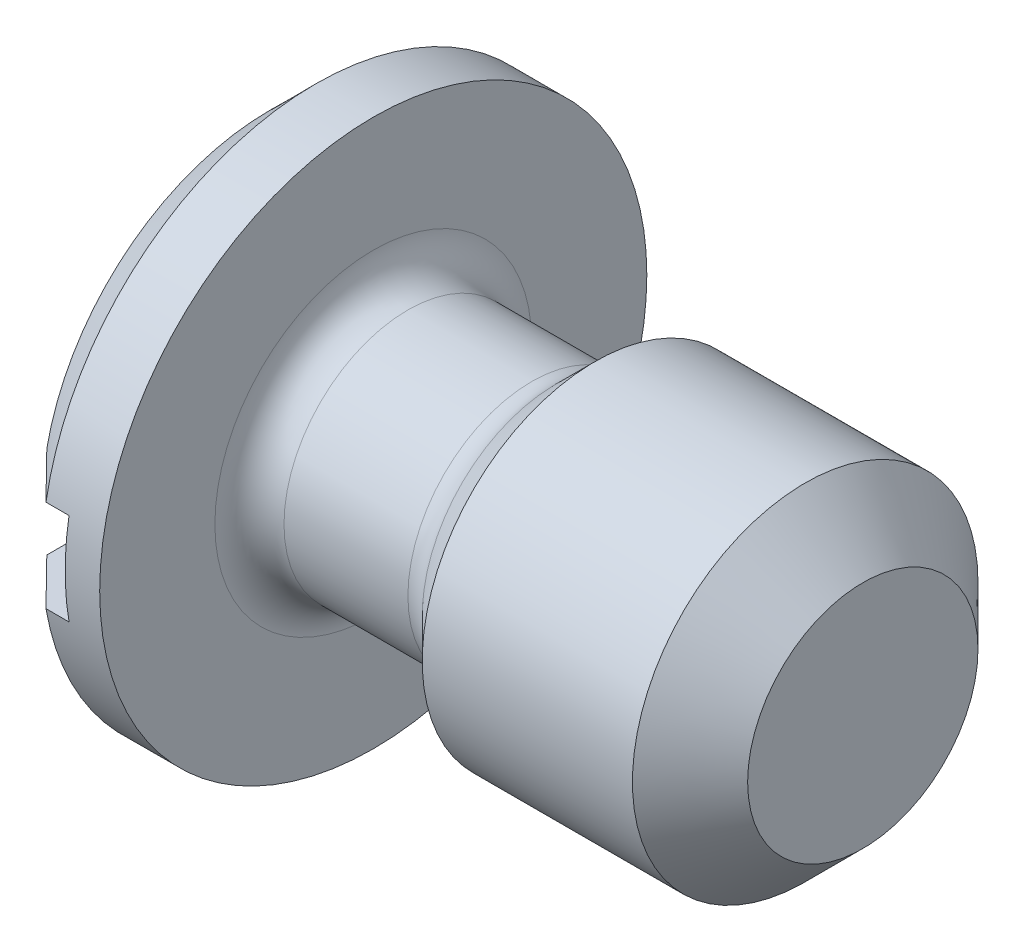
SolidWorks part; units mm, degrees
material "Сплав 3М ОСТ 1.92077-91"
ref_plane "Plane1" through (0, 0, 0) normal (0, 0, 1) x (1, 0, 0)
ref_plane "Plane2" through (0, 0, 0) normal (0, 1, 0) x (1, 0, 0)
ref_plane "Plane3" through (0, 0, 0) normal (1, 0, 0) x (0, 0, -1)
sketch "Эскиз1" plane through (0, 0, 0) normal (0, 0, 1) x (1, 0, 0)
  line L0 (0, 0) -> (-4.9956, 0) construction
  line L1 (0, 0) -> (0, 4.75)
  line L2 (0, 4.75) -> (1.8, 4.75)
  line L3 (1.8, 4.75) -> (1.8, 2.15)
  line L4 (1.8, 2.15) -> (4.8, 2.15)
  line L5 (4.8, 2.15) -> (5.65, 3)
  line L6 (5.65, 3) -> (10.3, 3)
  line L7 (10.3, 3) -> (10.3, 0)
  line L8 (10.3, 0) -> (0, 0)
  dimension "D1" = 4.3
  dimension "D2" = 3
  dimension "D3" = 6
  dimension "D4" = 8.5
  dimension "D5" = 45
  dimension "D6" = 10.3
  dimension "D7" = 9.5
revolve "Повернуть1" add sketch "Эскиз1" angle 360 about L0
cosmetic thread "Условное изображение резьбы1" parameters "D2"=5
chamfer "Фаска1" distance 1 angle 45 1 edges at (10.3, 0, -3)
fillet "Скругление1" radius 0.6 2 edges at (4.8, 0, -2.15) (1.8, 0, -2.15)
chamfer "Фаска2" distance 0.8 angle 45 1 edges at (0, 0, -4.75)
sketch "Эскиз2" plane through (0, 0, 0) normal (0, 0, 1) x (1, 0, 0)
  line L0 (0, 3.95) -> (0, -3.95) construction
  line L1 (0, 0.8) -> (1.2, 0.8)
  line L2 (0, 0.8) -> (0, -0.8)
  line L3 (0, -0.8) -> (1.2, -0.8)
  line L4 (1.2, 0.8) -> (1.2, -0.8)
  dimension "D1" = 1.6
  dimension "D2" = 1.2
extrude "Вырез-Вытянуть1" cut sketch "Эскиз2" against normal through all both and the other way through all
